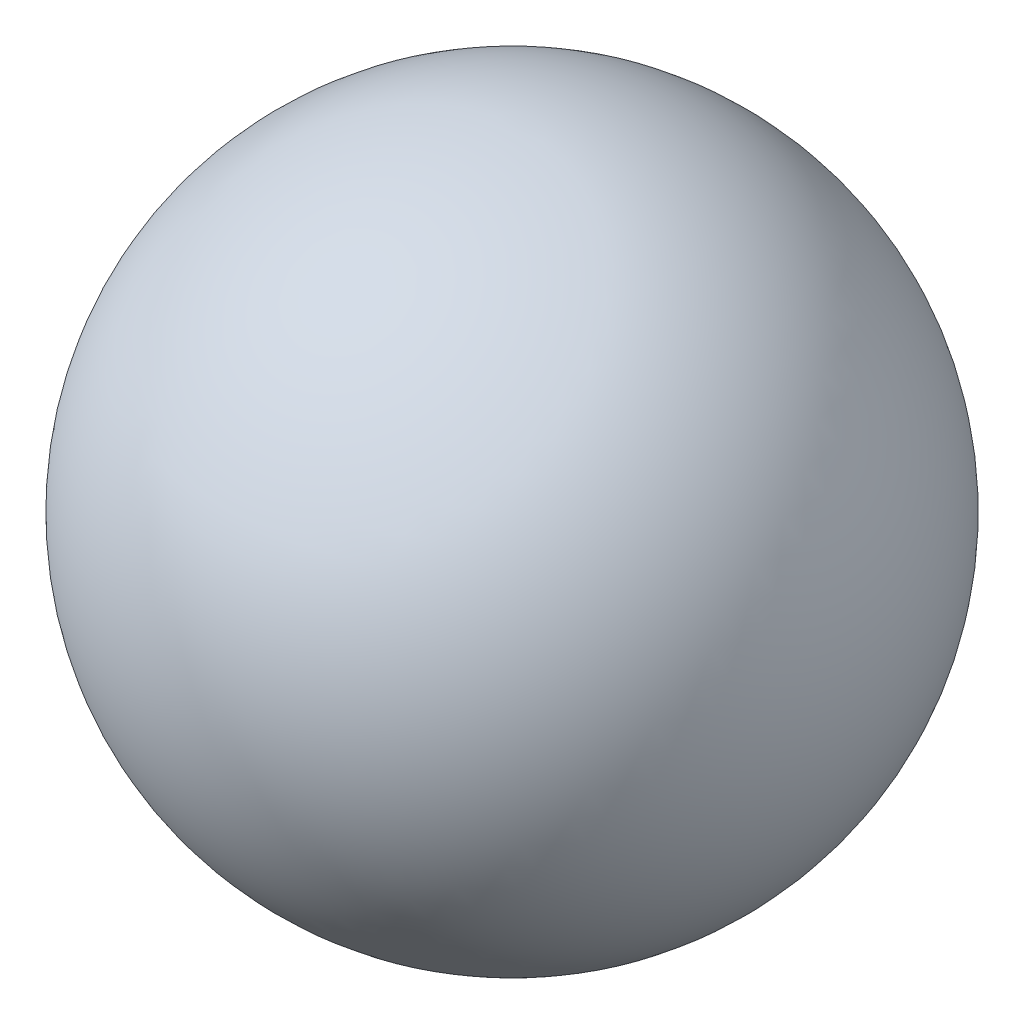
SolidWorks part; units mm, degrees
ref_plane "Спереди" through (0, 0, 0) normal (0, 0, 1) x (1, 0, 0)
ref_plane "Сверху" through (0, 0, 0) normal (0, 1, 0) x (1, 0, 0)
ref_plane "Справа" through (0, 0, 0) normal (1, 0, 0) x (0, 0, -1)
sketch "Эскиз1" plane through (0, 0, 0) normal (0, 0, 1) x (1, 0, 0)
  line L0 (0, 94.243) -> (0, -94.243)
  line L1 (0, 103.4354) -> (0, -102.3649) construction
  arc A0 (0, -94.243) -> (0, 94.243) centre (0, 0) ccw
revolve "Повернуть1" add sketch "Эскиз1" angle 360 about L1
